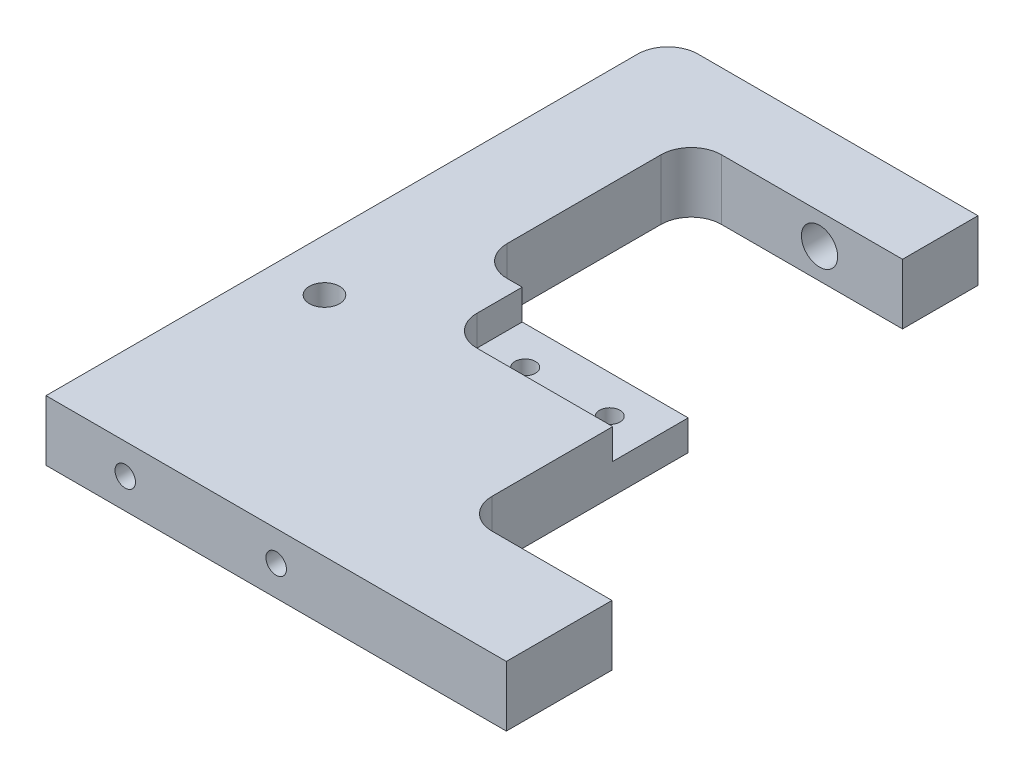
SolidWorks part; units mm, degrees
material "Unlegierter Baustahl"
ref_plane "Vorne" through (0, 0, 0) normal (0, 0, 1) x (1, 0, 0)
ref_plane "Oben" through (0, 0, 0) normal (0, 1, 0) x (1, 0, 0)
ref_plane "Rechts" through (0, 0, 0) normal (1, 0, 0) x (0, 0, -1)
sketch "Skizze1" plane through (0, 0, 0) normal (0, 1, 0) x (1, 0, 0)
  line L0 (0, 0) -> (0, 196)
  line L1 (0, -55) -> (0, 55) construction
  line L2 (152.5, 35) -> (112.75, 35)
  line L3 (10, 206) -> (102.75, 206)
  line L4 (102.75, 206) -> (102.75, 181)
  line L5 (102.75, 181) -> (42.75, 181)
  line L6 (32.75, 171) -> (32.75, 120)
  line L7 (42.75, 110) -> (102.75, 110)
  line L8 (102.75, 110) -> (102.75, 45)
  line L9 (-55, 0) -> (55, 0) construction
  line L10 (102.75, 0) -> (0, 0)
  line L11 (0, -17.9143) -> (0, 108.5516) construction
  line L12 (-27.6537, 0) -> (99.3909, 0) construction
  line L13 (37.9668, 35) -> (141.5756, 35) construction
  line L14 (152.5, 53.0144) -> (152.5, -17.9143) construction
  line L15 (102.75, 0) -> (152.5, 0)
  line L16 (152.5, 0) -> (152.5, 35)
  arc A0 (10, 206) -> (0, 196) centre (10, 196) ccw
  arc A1 (42.75, 181) -> (32.75, 171) centre (42.75, 171) ccw
  arc A2 (32.75, 120) -> (42.75, 110) centre (42.75, 120) ccw
  arc A3 (112.75, 35) -> (102.75, 45) centre (112.75, 45) cw
  point P30 (32.75, 110)
  point P33 (102.75, 35)
  dimension "D4" = 10
  dimension "D10" = 10
  dimension "D2" = 206
  dimension "D3" = 102.75
  dimension "D5" = 25
  dimension "D6" = 70
  dimension "D7" = 71
  dimension "D8" = 35
  dimension "D9" = 49.75
  dimension "D12" = 152.5
extrude "Linear austragen1" add sketch "Skizze1" along normal blind 20
sketch "Skizze20" plane through (0, 20, 0) normal (0, 1, 0) x (1, 0, 0)
  line L0 (47.75, 110) -> (47.75, 95)
  line L1 (102.75, 110) -> (42.75, 110) construction
  line L2 (57.75, 85) -> (102.75, 85)
  line L3 (102.75, 45) -> (102.75, 110) construction
  line L4 (47.75, 110) -> (102.75, 110)
  line L5 (102.75, 110) -> (102.75, 85)
  arc A0 (47.75, 95) -> (57.75, 85) centre (57.75, 95) ccw
  dimension "D1" = 10
  dimension "D2" = 55
  dimension "D3" = 25
extrude "Linear austragen2" cut sketch "Skizze20" against normal blind 10
hole_wizard "Ø12.0 (12) Durchmesser Bohrung1" positions "Skizze6" profile "Skizze7" hole size "Ø12.0" standard "DIN" end condition up to next
sketch "Skizze6" plane through (0, 0, -206) normal (0, 0, -1) x (-1, 0, 0)
  line L0 (-102.75, 10) -> (-34.7804, 10) construction
  line L1 (-102.75, 20) -> (-102.75, 0) construction
  point P0 (-75.25, 10)
  dimension "D1" = 27.5
sketch "Skizze7" plane through (75.25, 10, -206) normal (1, 0, 0) x (0, 1, 0)
  line L0 (0, 0) -> (0, 25)
  line L1 (0, 25) -> (6, 25)
  line L2 (6, 25) -> (6, 0)
  line L5 (6, 0) -> (0, 0)
  line L11 (0, -6.35) -> (0, 107.95) construction
  dimension "Bohrerdurchmesser" = 12
  dimension "Bohrungstiefe" = 25
hole_wizard "Ø10.0 (10) Durchmesser Bohrung1" positions "Skizze8" profile "Skizze9" hole size "Ø10.0" standard "DIN" end condition through all
sketch "Skizze8" plane through (51, 20, 10) normal (0, 1, 0) x (1, 0, 0)
  line L0 (-39.176, 47.5) -> (-10.3384, 47.5) construction
  line L3 (-32.5, 55) -> (-32.5, 40) construction
  line L6 (-32.5, 55) -> (-23.0833, 55) construction
  line L10 (-32.5, 40) -> (-23.8911, 40) construction
  line L11 (-62, 10) -> (-40, 10) construction
  line L12 (-51, -1) -> (-51, 21) construction
  point P0 (-33.75, 85)
  dimension "D1" = 75
  dimension "D2" = 17.25
sketch "Skizze9" plane through (17.25, 20, -75) normal (1, 0, 0) x (0, 0, 1)
  line L0 (0, 0) -> (0, 20)
  line L1 (0, 20) -> (5, 20)
  line L2 (5, 20) -> (5, 0)
  line L5 (5, 0) -> (0, 0)
  line L11 (0, -6.35) -> (0, 107.95) construction
  dimension "Bohrerdurchmesser" = 10
  dimension "Bohrungstiefe" = 20
hole_wizard "M6 Gewindebohrung1" positions "Skizze13" profile "Skizze12" tap size "M6" standard "DIN"
sketch "Skizze13" plane through (0, 0, 0) normal (-1, 0, 0) x (0, 0, 1)
  line L0 (0, 10) -> (-53.8388, 10) construction
  line L1 (0, 20) -> (0, 0) construction
  line L7 (0, -11) -> (0, 11) construction
  point P0 (-75, 10)
  dimension "D1" = 75
sketch "Skizze12" plane through (0, 10, -75) normal (0, 1, 0) x (0, 0, 1)
  line L0 (0, 0) -> (0, 12.25)
  line L1 (0, 12.25) -> (2.5, 12.25)
  line L2 (2.5, 12.25) -> (2.5, 0)
  line L5 (2.5, 0) -> (0, 0)
  line L11 (0, -6.35) -> (0, 107.95) construction
  dimension "Bohrerdurchmesser" = 5
  dimension "Bohrungstiefe" = 12.25
cosmetic thread "Bohrungsgewinde1" parameters "D2"=6
hole_wizard "M8 Gewindebohrung1" positions "Skizze14" profile "Skizze15" tap size "M8" standard "DIN"
sketch "Skizze14" plane through (51.25, 10, 0) normal (0, 0, 1) x (1, 0, 0)
  line L0 (-51.25, 0) -> (35.1205, 0) construction
  line L4 (-51.25, 10) -> (-51.25, -10) construction
  point P1 (-25, 0)
  point P13 (25, 0)
  dimension "D1" = 26.25
  dimension "D2" = 50
sketch "Skizze15" plane through (26.25, 10, 0) normal (1, 0, 0) x (0, -1, 0)
  line L0 (0, 0) -> (0, 24.2929)
  line L1 (0, 24.2929) -> (3.4, 22.25)
  line L2 (3.4, 22.25) -> (3.4, 0)
  line L5 (3.4, 0) -> (0, 0)
  line L10 (0, 24.2929) -> (-3.4, 22.25) construction
  line L11 (0, -6.35) -> (0, 107.95) construction
  dimension "Bohrerdurchmesser" = 6.8
  dimension "Bohrungstiefe" = 22.25
  dimension "Spitzenwinkel" = 118
cosmetic thread "Bohrungsgewinde20" parameters "D1"=16, "D2"=8
cosmetic thread "Bohrungsgewinde21" parameters "D1"=16, "D2"=8
hole_wizard "M6 Gewindebohrung3" positions "Skizze19" profile "Skizze18" tap size "M6" standard "DIN"
sketch "Skizze19" plane through (6.2095, 2.15, -35) normal (0, 0, -1) x (-1, 0, 0)
  line L0 (-146.2905, 17.85) -> (-146.2905, -2.15) construction
  line L1 (-146.2905, 7.85) -> (-106.5405, 7.85) construction
  line L2 (-106.5405, 17.85) -> (-106.5405, -2.15) construction
  point P1 (-137.2905, 7.85)
  point P4 (-124.7905, 7.85)
  point P8 (-146.2905, 7.85)
  dimension "D1" = 21.5
  dimension "D2" = 12.5
sketch "Skizze18" plane through (143.5, 10, -35) normal (1, 0, 0) x (0, 1, 0)
  line L0 (0, 0) -> (0, 18.5022)
  line L1 (0, 18.5022) -> (2.5, 17)
  line L2 (2.5, 17) -> (2.5, 0)
  line L5 (2.5, 0) -> (0, 0)
  line L10 (0, 18.5022) -> (-2.5, 17) construction
  line L11 (0, -6.35) -> (0, 107.95) construction
  dimension "Bohrerdurchmesser" = 5
  dimension "Bohrungstiefe" = 17
  dimension "Spitzenwinkel" = 118
cosmetic thread "Bohrungsgewinde16" parameters "D1"=12, "D2"=6
cosmetic thread "Bohrungsgewinde17" parameters "D1"=12, "D2"=6
hole_wizard "M8 Gewindebohrung2" positions "Skizze22" profile "Skizze21" tap size "M8" standard "DIN"
sketch "Skizze22" plane through (0, 10, 0) normal (0, 1, 0) x (-1, 0, 0)
  line L0 (-102.75, -85) -> (-102.75, -110) construction
  line L1 (-102.75, -110) -> (-47.75, -110) construction
  point P0 (-61.25, -97.5)
  point P1 (-89.25, -97.5)
  point P4 (-102.75, -97.5)
  dimension "D1" = 41.5
  dimension "D2" = 13.5
  dimension "D3" = 12.5
sketch "Skizze21" plane through (61.25, 10, -97.5) normal (1, 0, 0) x (0, 0, 1)
  line L0 (0, 0) -> (0, 24.2929)
  line L1 (0, 24.2929) -> (3.4, 22.25)
  line L2 (3.4, 22.25) -> (3.4, 0)
  line L5 (3.4, 0) -> (0, 0)
  line L10 (0, 24.2929) -> (-3.4, 22.25) construction
  line L11 (0, -6.35) -> (0, 107.95) construction
  dimension "Bohrerdurchmesser" = 6.8
  dimension "Bohrungstiefe" = 22.25
  dimension "Spitzenwinkel" = 118
cosmetic thread "Bohrungsgewinde18" parameters "D1"=10, "D2"=8
cosmetic thread "Bohrungsgewinde19" parameters "D1"=10, "D2"=8
